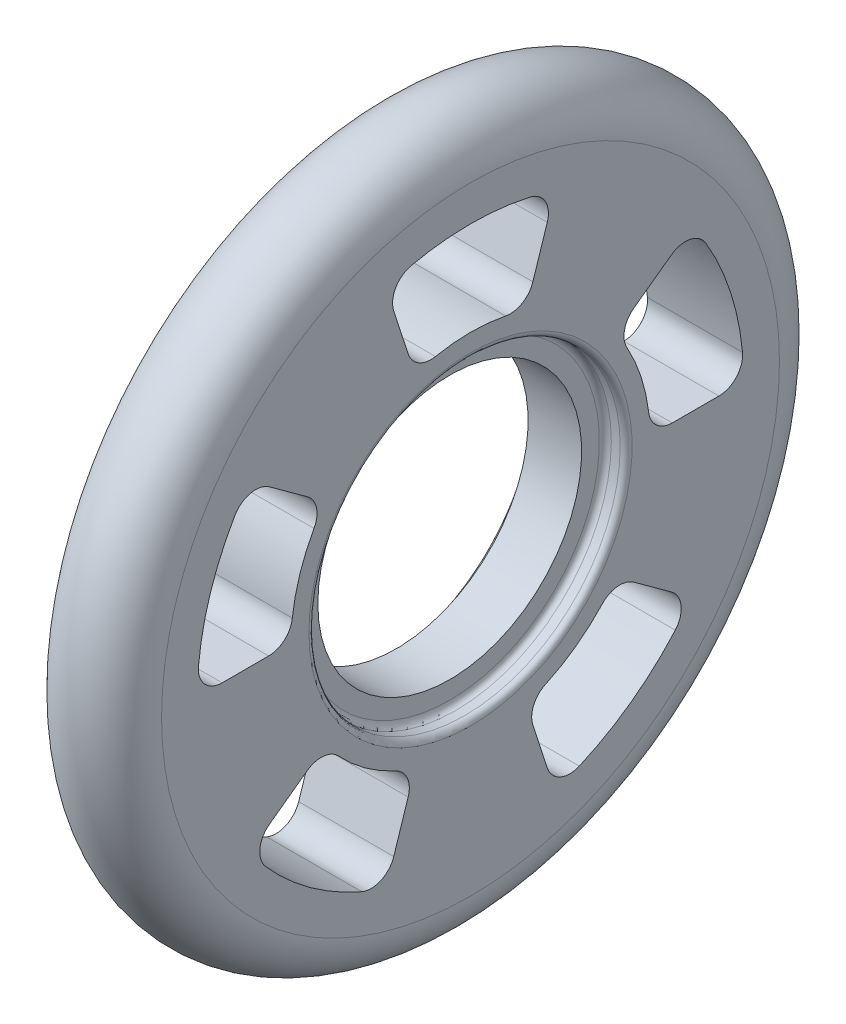
SolidWorks part; units mm, degrees
ref_plane "Front Plane" through (0, 0, 0) normal (0, 0, 1) x (1, 0, 0)
ref_plane "Top Plane" through (0, 0, 0) normal (0, 1, 0) x (1, 0, 0)
ref_plane "Right Plane" through (0, 0, 0) normal (1, 0, 0) x (0, 0, -1)
sketch "Sketch3" plane through (0, 0, 0) normal (0, 0, 1) x (1, 0, 0)
  line L0 (0, 0) -> (10.5995, 0) construction
  line L1 (0, 0) -> (0, 26) construction
  line L2 (-2.25, 11.1) -> (2.25, 11.1)
  line L3 (2.25, 11.1) -> (2.25, 12.6)
  line L4 (2.75, 13.1) -> (3.5, 13.1)
  line L5 (4, 13.6) -> (4, 26)
  line L6 (-4, 13.6) -> (-4, 26)
  line L7 (-2.75, 13.1) -> (-3.5, 13.1)
  line L8 (-2.25, 11.1) -> (-2.25, 12.6)
  arc A0 (2.25, 12.6) -> (2.75, 13.1) centre (2.75, 12.6) cw
  arc A1 (3.5, 13.1) -> (4, 13.6) centre (3.5, 13.6) ccw
  arc A4 (-3.5, 13.1) -> (-4, 13.6) centre (-3.5, 13.6) cw
  arc A5 (-2.25, 12.6) -> (-2.75, 13.1) centre (-2.75, 12.6) ccw
  arc A6 (4, 26) -> (-4, 26) centre (0, 26) ccw
  point P3 (-2.25, 11.1)
  point P4 (0, 30)
  point P12 (2.25, 13.1)
  point P15 (4, 13.1)
  point P18 (2.25, 11.1)
  point P29 (0, 11.1)
  point P30 (-4, 13.1)
  point P31 (-2.25, 13.1)
  dimension "D6" = 0.5
  dimension "D1" = 2.25
  dimension "D2" = 11.1
  dimension "D3" = 30
  dimension "D4" = 4
  dimension "D5" = 2
revolve "Revolve1" add sketch "Sketch3" angle 360 about L0
sketch "Sketch6" plane through (4, 0, 0) normal (1, 0, 0) x (0, 0, -1)
  line L0 (13.7392, 9.9821) -> (16.9121, 12.2874)
  line L1 (20.9045, 0) -> (16.9826, 0)
  line L2 (0, 0) -> (19.5288, 0) construction
  line L3 (0, 0) -> (0, 5.2799) construction
  line L4 (23, 0) -> (0, 0) construction
  line L5 (18.6074, 13.5191) -> (0, 0) construction
  circle A0 centre (0, 0) radius 13.6 construction
  arc A2 (13.1704, 7.3859) -> (14.9964, 1.7661) centre (0, 0) cw
  arc A3 (19.8103, 11.6855) -> (22.8955, 2.1905) centre (0, 0) cw
  circle A4 centre (0, 0) radius 26 construction
  arc A5 (16.9826, 0) -> (14.9964, 1.7661) centre (16.9826, 2) cw
  arc A6 (13.7392, 9.9821) -> (13.1704, 7.3859) centre (14.9148, 8.3641) ccw
  arc A7 (20.9045, 0) -> (22.8955, 2.1905) centre (20.9045, 2) ccw
  arc A8 (16.9121, 12.2874) -> (19.8103, 11.6855) centre (18.0877, 10.6693) cw
  dimension "D1" = 36
  dimension "D3" = 1.5
  dimension "D4" = 3
  dimension "D2" = 2
extrude "Cut-Extrude1" cut sketch "Sketch6" against normal up to next (8 mm away)
pattern_circular "CirPattern1" count 5 over 360 about axis through (0, 0, 0) along (1, 0, 0) of "Cut-Extrude1"
